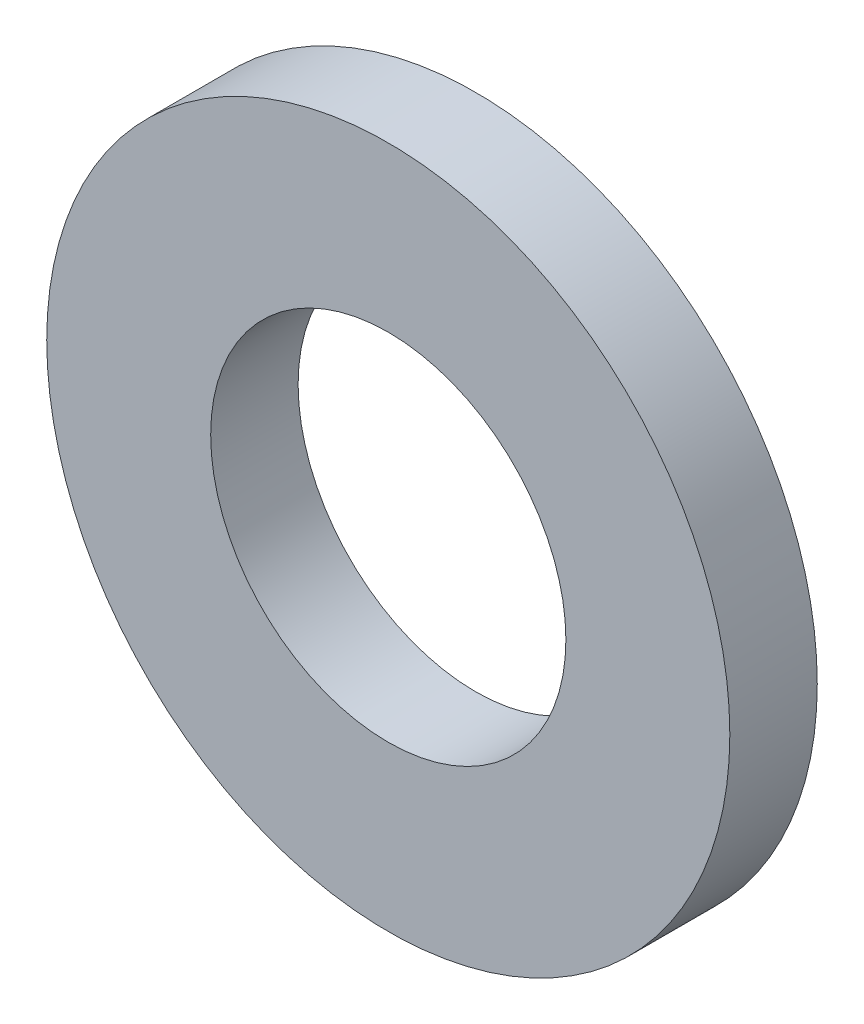
SolidWorks part; units mm, degrees
ref_plane "Front Plane" through (0, 0, 0) normal (0, 0, 1) x (1, 0, 0)
ref_plane "Top Plane" through (0, 0, 0) normal (0, 1, 0) x (1, 0, 0)
ref_plane "Right Plane" through (0, 0, 0) normal (1, 0, 0) x (0, 0, -1)
sketch "Sketch1" plane through (0, 0, 0) normal (0, 0, 1) x (1, 0, 0)
  circle A0 centre (0, 0) radius 6.25
  circle A1 centre (0, 0) radius 3.25
  dimension "D1" = 12.5
  dimension "D2" = 6.5
extrude "Boss-Extrude1" add sketch "Sketch1" along normal blind 1.6
